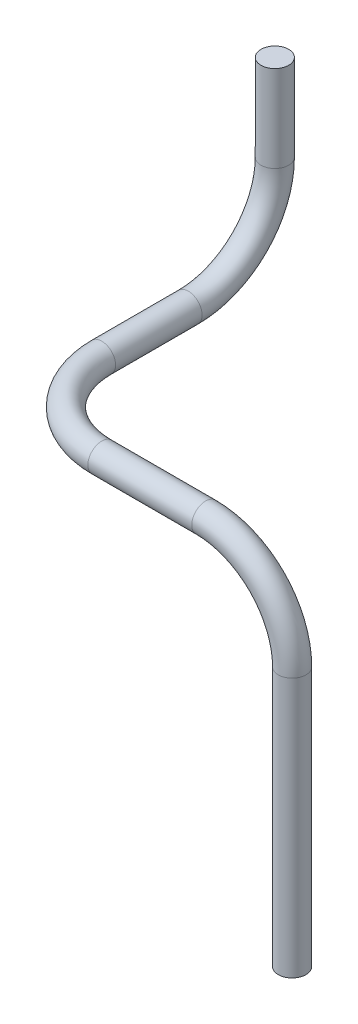
SolidWorks part; units mm, degrees
ref_plane "Front Plane" through (0, 0, 0) normal (0, 0, 1) x (1, 0, 0)
ref_plane "Top Plane" through (0, 0, 0) normal (0, 1, 0) x (1, 0, 0)
ref_plane "Right Plane" through (0, 0, 0) normal (1, 0, 0) x (0, 0, -1)
sketch "Sketch1" plane through (0, 0, 0) normal (0, 1, 0) x (1, 0, 0)
  circle A4 centre (0, 0) radius 0.8
  dimension "D1" = 1.6
sketch3d "3DSketch1"
  line L0 (0, 0, 0) -> (0, -10, 0) construction
  line L1 (0, -10, 0) -> (0, -10, 15) construction
  line L2 (0, -10, 15) -> (16, -10, 15) construction
  line L3 (16, -10, 15) -> (16, -30, 15) construction
  line L4 (0, 0, 0) -> (0, -5, 0)
  line L5 (0, -10, 5) -> (0, -10, 10)
  line L6 (5, -10, 15) -> (11, -10, 15)
  line L7 (16, -15, 15) -> (16, -30, 15)
  arc A0 (0, -5, 0) -> (0, -10, 5) centre (0, -5, 5) ccw
  arc A1 (0, -10, 10) -> (5, -10, 15) centre (5, -10, 10) ccw
  arc A2 (11, -10, 15) -> (16, -15, 15) centre (11, -15, 15) ccw
  point P8 (-5, -5, 5)
  point P16 (5, -5, 10)
  point P18 (11, -15, 10)
  dimension "D5" = 5
  dimension "D6" = 5
  dimension "D7" = 5
  dimension "D1" = 10
  dimension "D2" = 15
  dimension "D3" = 16
  dimension "D4" = 20
sweep "Sweep1" add profiles "Sketch1" path "3DSketch1"
